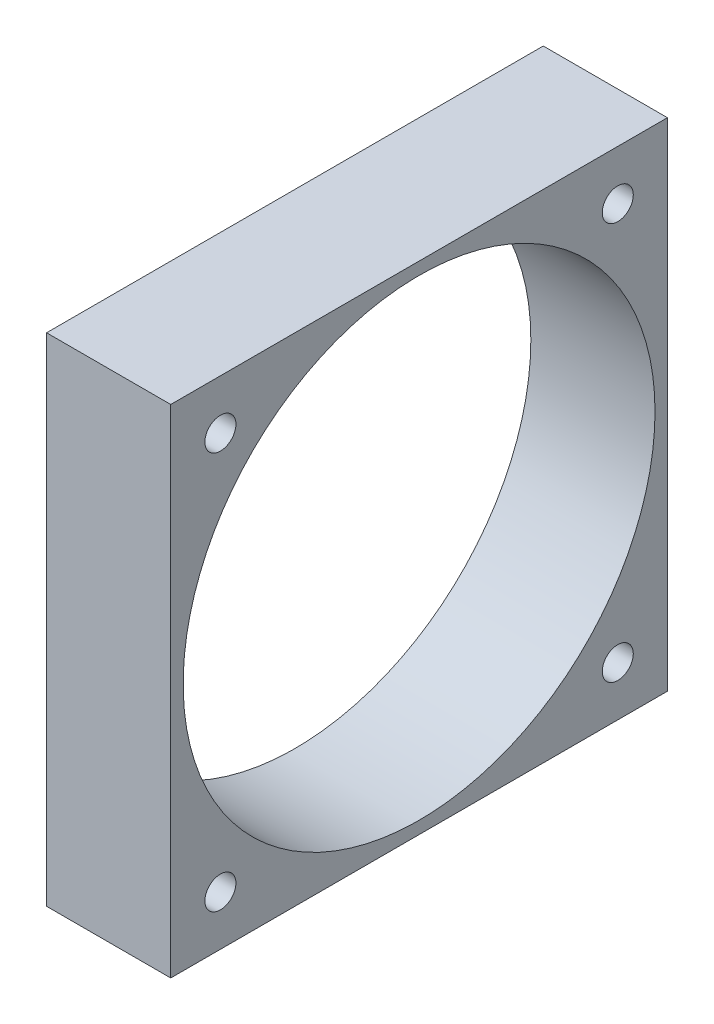
SolidWorks part; units mm, degrees
ref_plane "Front Plane" through (0, 0, 0) normal (0, 0, 1) x (1, 0, 0)
ref_plane "Top Plane" through (0, 0, 0) normal (0, 1, 0) x (1, 0, 0)
ref_plane "Right Plane" through (0, 0, 0) normal (1, 0, 0) x (0, 0, -1)
sketch "Sketch1" plane through (0, 0, 0) normal (1, 0, 0) x (0, 0, -1)
  line L1 (-20, 20) -> (20, 20)
  line L2 (-20, 20) -> (-20, -20)
  line L3 (-20, -20) -> (20, -20)
  line L4 (20, 20) -> (20, -20)
  line L5 (-20, 20) -> (20, -20) construction
  line L6 (-20, -20) -> (20, 20) construction
  circle A0 centre (0, 0) radius 19
  circle A1 centre (-16, 16) radius 1.25
  circle A2 centre (16, 16) radius 1.25
  circle A3 centre (16, -16) radius 1.25
  circle A4 centre (-16, -16) radius 1.25
  point P0 (0, 0)
  point P19 (0, 0)
  dimension "D3" = 2.5
  dimension "D5" = 32
  dimension "D6" = 38
  dimension "D1" = 40
  dimension "D2" = 40
  dimension "D4" = 4
extrude "Boss-Extrude1" add sketch "Sketch1" along normal blind 10
